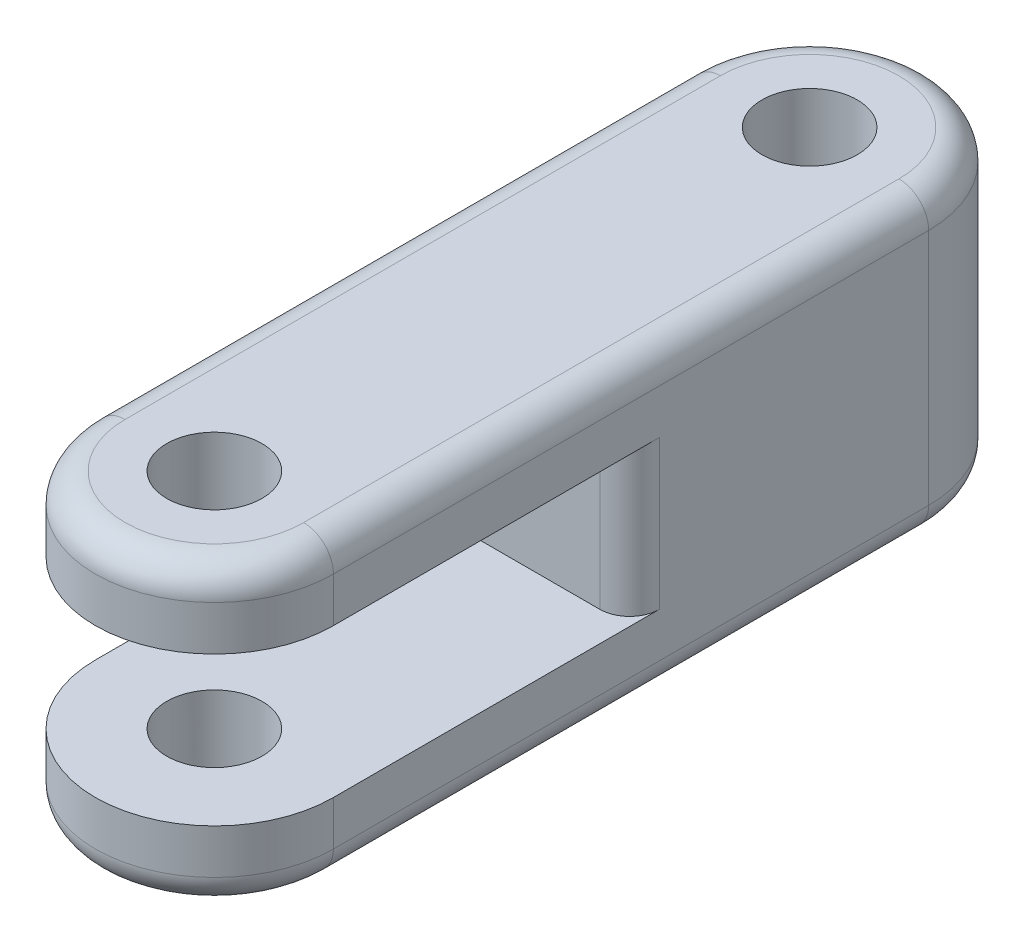
SolidWorks part; units mm, degrees
ref_plane "前视基准面" through (0, 0, 0) normal (0, 0, 1) x (1, 0, 0)
ref_plane "上视基准面" through (0, 0, 0) normal (0, 1, 0) x (1, 0, 0)
ref_plane "右视基准面" through (0, 0, 0) normal (1, 0, 0) x (0, 0, -1)
sketch "草图1" plane through (0, 0, 0) normal (0, 1, 0) x (1, 0, 0)
  line L0 (0, 0) -> (0, 20) construction
  line L1 (-4, 0) -> (-4, 20)
  line L2 (4, 0) -> (4, 20)
  arc A0 (-4, 0) -> (4, 0) centre (0, 0) ccw
  arc A1 (4, 20) -> (-4, 20) centre (0, 20) ccw
  circle A2 centre (0, 20) radius 1.6
  circle A3 centre (0, 0) radius 1.6
  point P3 (0, 10)
  dimension "D2" = 4
  dimension "D1" = 20
extrude "凸台-拉伸1" add sketch "草图1" along normal blind 10
sketch "草图2" plane through (4, 0, 0) normal (1, 0, 0) x (0, 0, -1)
  line L0 (0, 10) -> (0, 0) construction
  line L1 (9.9497, 2.5) -> (-9.9497, 2.5)
  line L2 (9.9497, 2.5) -> (9.9497, 7.5)
  line L3 (9.9497, 7.5) -> (-9.9497, 7.5)
  line L4 (-9.9497, 2.5) -> (-9.9497, 7.5)
  line L5 (9.9497, 2.5) -> (-9.9497, 7.5) construction
  line L6 (9.9497, 7.5) -> (-9.9497, 2.5) construction
  point P0 (0, 5)
  dimension "D1" = 5
extrude "切除-拉伸1" cut sketch "草图2" against normal blind 10
fillet "圆角1" radius 1 10 edges at (0, 0, 4) (4, 0, -10) (0, 0, -24) (0, 10, 4) (-4, 10, -10) (0, 10, -24) (4, 5, -9.9497) (-4, 5, -9.9497) (-4, 0, -10) (4, 10, -10)
